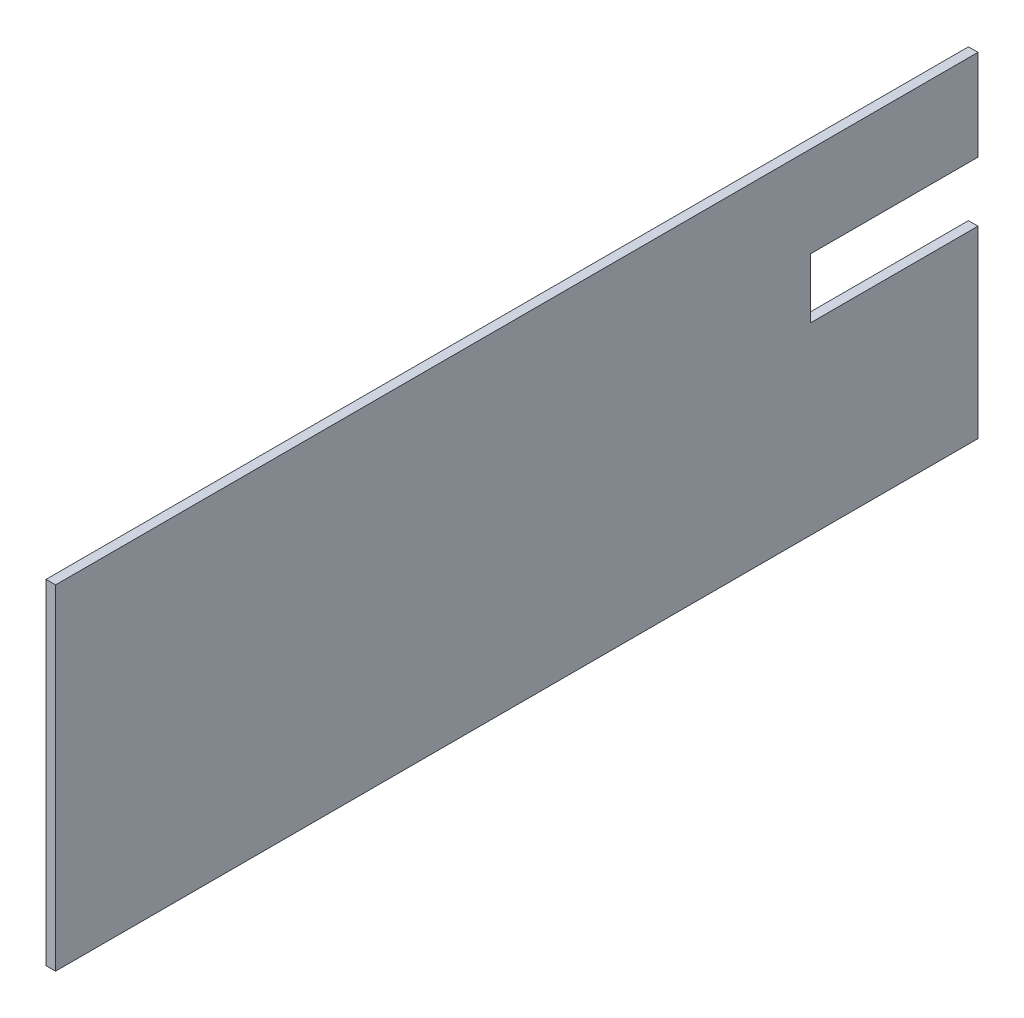
SolidWorks part; units mm, degrees
ref_plane "Front Plane" through (0, 0, 0) normal (0, 0, 1) x (1, 0, 0)
ref_plane "Top Plane" through (0, 0, 0) normal (0, 1, 0) x (1, 0, 0)
ref_plane "Right Plane" through (0, 0, 0) normal (1, 0, 0) x (0, 0, -1)
sketch "Sketch1" plane through (0, 0, 0) normal (1, 0, 0) x (0, 0, -1)
  line L1 (0, 0) -> (193, 0)
  line L2 (0, 0) -> (0, 70)
  line L3 (0, 70) -> (193, 70)
  line L4 (193, 0) -> (193, 70)
  dimension "D1" = 193
  dimension "D2" = 70
extrude "Boss-Extrude1" add sketch "Sketch1" along normal blind 35
sketch "Sketch2" plane through (0, 0, 0) normal (0, 0, 1) x (1, 0, 0)
  line L0 (35, 70) -> (35, 0) construction
  line L1 (0, 70) -> (33, 70)
  line L2 (0, 70) -> (0, 0)
  line L3 (0, 0) -> (33, 0)
  line L4 (33, 70) -> (33, 0)
  line L5 (35, 0) -> (0, 0) construction
  dimension "D1" = 2
  dimension "D2" = 0
extrude "Cut-Extrude1" cut sketch "Sketch2" against normal through all
sketch "Sketch3" plane through (35, 0, 0) normal (1, 0, 0) x (0, 0, -1)
  line L1 (193, 0) -> (193, 70) construction
  line L2 (193, 51) -> (158, 51)
  line L3 (193, 51) -> (193, 38.5)
  line L4 (193, 38.5) -> (158, 38.5)
  line L7 (158, 51) -> (158, 38.5)
  line L8 (193, 70) -> (0, 70) construction
  dimension "D1" = 19
  dimension "D2" = 12.5
  dimension "D3" = 35
extrude "Cut-Extrude2" cut sketch "Sketch3" against normal blind 10
